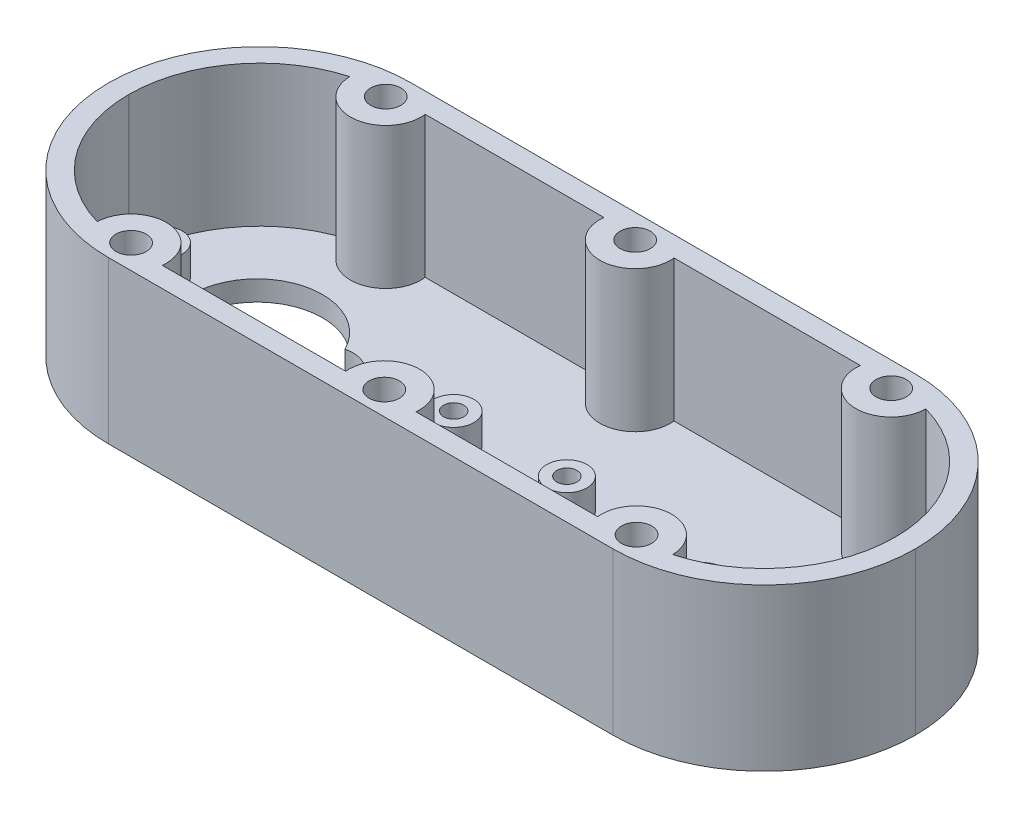
SolidWorks part; units mm, degrees
ref_plane "Front Plane" through (0, 0, 0) normal (0, 0, 1) x (1, 0, 0)
ref_plane "Top Plane" through (0, 0, 0) normal (0, 1, 0) x (1, 0, 0)
ref_plane "Right Plane" through (0, 0, 0) normal (1, 0, 0) x (0, 0, -1)
sketch "Sketch3" plane through (0, 0, 0) normal (0, 1, 0) x (1, 0, 0)
  line L1 (-7.5913, 15.7627) -> (42.4287, 15.7627)
  line L2 (-22.5813, 0.7727) -> (-22.5813, 0.7527)
  line L3 (-7.5913, -14.2373) -> (42.4287, -14.2373)
  line L4 (57.4187, 0.7727) -> (57.4187, 0.7527)
  arc A0 (42.4287, 15.7627) -> (57.4187, 0.7727) centre (42.4287, 0.7727) cw
  arc A1 (57.4187, 0.7527) -> (42.4287, -14.2373) centre (42.4287, 0.7527) cw
  arc A2 (-7.5913, -14.2373) -> (-22.5813, 0.7527) centre (-7.5913, 0.7527) cw
  arc A3 (-22.5813, 0.7727) -> (-7.5913, 15.7627) centre (-7.5913, 0.7727) cw
  circle A4 centre (-7.6551, 13.3205) radius 1.5
  circle A5 centre (-7.7287, -11.8524) radius 1.5
  circle A6 centre (17.4187, -11.8982) radius 1.5
  circle A7 centre (17.0064, 13.3885) radius 1.5
  circle A8 centre (42.4287, 13.3427) radius 1.5
  circle A9 centre (42.3829, -11.8524) radius 1.5
  arc A18 (-2.0073, 2.8839) -> (-2.0073, -2.9541) centre (-7.815, -0.0351) ccw
  arc A19 (-2.0073, -2.9541) -> (-2.0073, 2.8839) centre (-1.315, -0.0351) ccw
  arc A22 (36.5905, -2.9432) -> (36.5905, 2.8949) centre (35.8982, -0.0242) cw
  arc A23 (36.5905, 2.8949) -> (36.5905, -2.9432) centre (42.3982, -0.0242) cw
  circle A24 centre (11.685, -0.0351) radius 2
  circle A25 centre (22.8982, -0.0242) radius 2
  point P8 (57.4187, -14.2373)
  point P11 (-22.5813, -14.2373)
  point P14 (-22.5813, 15.7627)
  dimension "D3" = 14.99
  dimension "D4" = 3
  dimension "D5" = 3
  dimension "D6" = 3
  dimension "D7" = 3
  dimension "D8" = 3
  dimension "D9" = 3
  dimension "D1" = 30
  dimension "D2" = 80
extrude "Boss-Extrude9" add sketch "Sketch3" along normal blind 16 contours A23 A22 | A3 L2 A2 L3 A1 L4 A0 L1 A25 A24 A19 A18 A9 A8 A7 A6 A5 A4 A22 A23 | A24 | A25
shell "Shell6" thickness 2
sketch "Sketch6" plane through (0, 2, 0) normal (0, 1, 0) x (1, 0, 0)
  line L0 (-20.5813, 0.7727) -> (-20.5813, 0.7527) construction
  line L1 (-4.25, -12.2373) -> (13.9352, -12.2373) construction
  arc A0 (-1.9967, 3.6214) -> (-1.9967, -2.2166) centre (-7.8044, 0.7024) ccw
  arc A1 (-1.9967, -2.2166) -> (-1.9967, 3.6214) centre (-1.3044, 0.7024) ccw
  arc A2 (36.6011, -2.2057) -> (36.6011, 3.6324) centre (35.9088, 0.7133) cw
  arc A3 (36.6011, 3.6324) -> (36.6011, -2.2057) centre (42.4088, 0.7133) cw
  circle A4 centre (11.6956, 0.7024) radius 1
  circle A5 centre (22.9088, 0.7133) radius 1
  dimension "D1" = 2
  dimension "D2" = 6.5
  dimension "D3" = 3
  dimension "D4" = 12.7769
  dimension "D5" = 56.4901
  dimension "D6" = 10.0207
  dimension "D7" = 32.2769
  dimension "D8" = 43.4901
  dimension "D9" = 10.0316
extrude "Cut-Extrude3" cut sketch "Sketch6" against normal blind 16 contours A3 A2 | A0 A1
sketch "Sketch12" plane through (0, 2, 0) normal (0, 1, 0) x (1, 0, 0)
  circle A0 centre (-17.2273, 0.7018) radius 1
  circle A2 centre (51.9503, 0.7018) radius 1
  circle A3 centre (51.9503, 0.7018) radius 2
  circle A4 centre (11.6956, 0.7024) radius 1
  circle A5 centre (22.9088, 0.7133) radius 1
  circle A6 centre (-17.2273, 0.7018) radius 2
  circle A7 centre (11.6956, 0.7024) radius 2
  circle A8 centre (22.9088, 0.7133) radius 2
  point P7 (0, 0)
extrude "Boss-Extrude16" add sketch "Sketch12" along normal blind 3 contours A3 | A2 | A5 | A8 | A7 | A4 | A0 | A6
